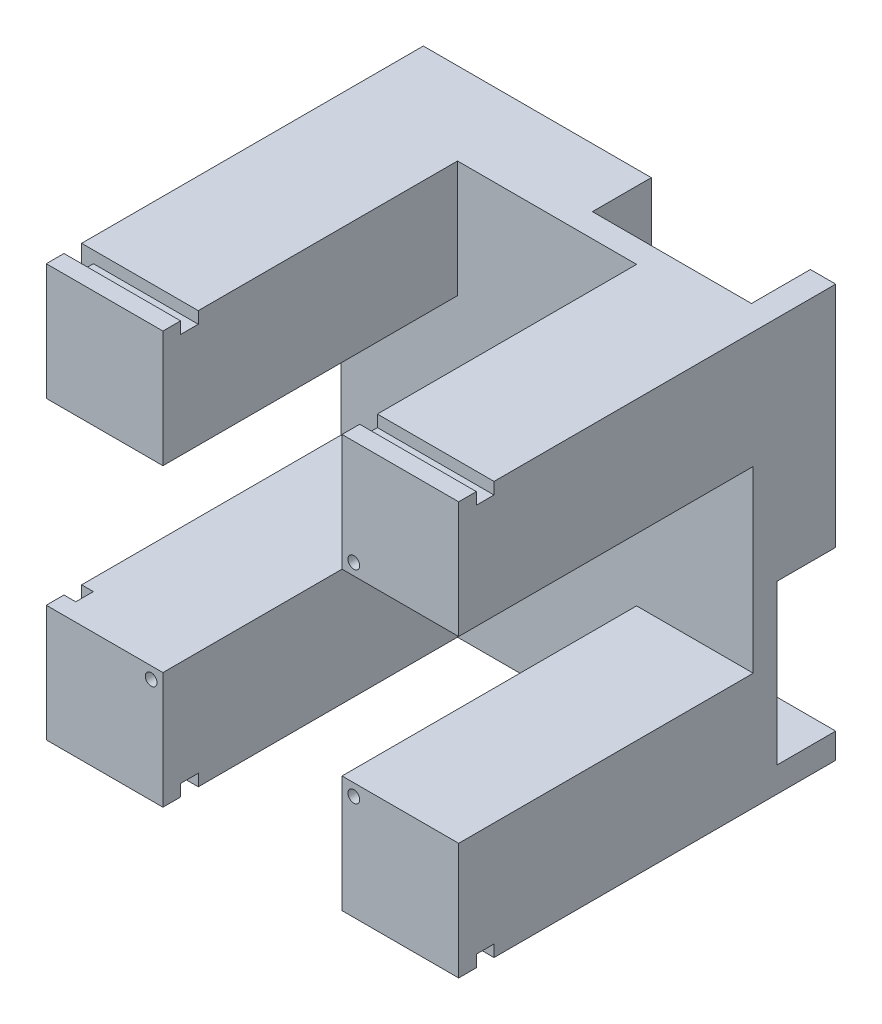
SolidWorks part; units mm, degrees
ref_plane "Plan de face" through (0, 0, 0) normal (0, 0, 1) x (1, 0, 0)
ref_plane "Plan de dessus" through (0, 0, 0) normal (0, 1, 0) x (1, 0, 0)
ref_plane "Plan de droite" through (0, 0, 0) normal (1, 0, 0) x (0, 0, -1)
sketch "Esquisse1" plane through (0, 0, 0) normal (0, 0, 1) x (1, 0, 0)
  line L1 (0, 0) -> (-70, 0)
  line L2 (0, 0) -> (0, 70)
  line L3 (0, 70) -> (-70, 70)
  line L4 (-70, 0) -> (-70, 70)
  dimension "D1" = 70
  dimension "D2" = 70
extrude "Boss.-Extru.1" add sketch "Esquisse1" along normal blind 64
sketch "Esquisse2" plane through (0, 0, 64) normal (0, 0, 1) x (1, 0, 0)
  line L0 (-70, 70) -> (-70, 0) construction
  line L1 (-70, 50.2) -> (0, 50.2)
  line L2 (-70, 50.2) -> (-70, 19.8)
  line L3 (-70, 19.8) -> (0, 19.8)
  line L4 (0, 50.2) -> (0, 19.8)
  line L5 (0, 0) -> (0, 70) construction
  line L6 (-70, 0) -> (0, 0) construction
  line L7 (-19.8, 0) -> (-50.2, 0)
  line L8 (-19.8, 0) -> (-19.8, 70)
  line L9 (-19.8, 70) -> (-50.2, 70)
  line L10 (-50.2, 0) -> (-50.2, 70)
  line L11 (0, 70) -> (-70, 70) construction
  line M5 (0, 0) -> (0, 70)
  line M6 (0, 70) -> (-70, 70)
  line M7 (-70, 70) -> (-70, 0)
  line M8 (-70, 0) -> (0, 0)
  dimension "D1" = 30.4
  dimension "D2" = 19.8
  dimension "D3" = 30.4
  dimension "D4" = 19.8
extrude "Enlèv. mat.-Extru.1" cut sketch "Esquisse2" against normal blind 50 contours L10 L1 L8 M6 | L10 L3 L8 L1 | L8 L3 L1 M5 | L3 L10 L1 M7 | L10 L8 L3 M8
sketch "Esquisse5" plane through (-70, 0, 0) normal (-1, 0, 0) x (0, 0, 1)
  line L0 (64, 70) -> (0, 70) construction
  line L1 (61, 70) -> (58, 70)
  line L2 (61, 70) -> (61, 68)
  line L3 (61, 68) -> (58, 68)
  line L4 (58, 70) -> (58, 68)
  line L5 (64, 0) -> (0, 0) construction
  line L6 (61, 0) -> (58, 0)
  line L7 (61, 0) -> (61, 2)
  line L8 (61, 2) -> (58, 2)
  line L9 (58, 0) -> (58, 2)
  line L10 (64, 19.8) -> (64, 0) construction
  line L11 (64, 70) -> (64, 50.2) construction
  dimension "D1" = 3
  dimension "D2" = 3
  dimension "D3" = 2
  dimension "D4" = 2
  dimension "D5" = 3
  dimension "D6" = 3
extrude "Enlèv. mat.-Extru.3" cut sketch "Esquisse5" against normal through all
sketch "Esquisse6" plane through (0, 70, 0) normal (0, 1, 0) x (1, 0, 0)
  line L0 (-50.2, -61) -> (-70, -61) construction
  line L1 (-70, -58) -> (-68, -58)
  line L2 (-70, -58) -> (-70, -61)
  line L3 (-70, -61) -> (-68, -61)
  line L4 (-68, -58) -> (-68, -61)
  dimension "D1" = 2
extrude "Enlèv. mat.-Extru.4" cut sketch "Esquisse6" against normal through all
sketch "Esquisse7" plane through (0, 0, 64) normal (0, 0, 1) x (1, 0, 0)
  line L0 (-50.2, 0) -> (-50.2, 19.8) construction
  line L1 (-70, 19.8) -> (-50.2, 19.8) construction
  circle A0 centre (-52.2, 17.8) radius 1
  dimension "D1" = 2
  dimension "D2" = 2
  dimension "D3" = 2
extrude "Enlèv. mat.-Extru.5" cut sketch "Esquisse7" against normal through all
sketch "Esquisse8" plane through (0, 0, 0) normal (0, 0, -1) x (-1, 0, 0)
  line L0 (60.2, 17.8) -> (60.2, 0)
  line L1 (70, 0) -> (0, 0) construction
  line L2 (60.2, 0) -> (44.2, 0)
  line L3 (44.2, 0) -> (44.2, 17.8)
  line L4 (44.2, 17.8) -> (60.2, 17.8)
  circle A0 centre (52.2, 17.8) radius 8
  circle M2 centre (52.2, 17.8) radius 1
  line M4 (0, 0) -> (70, 0)
  dimension "D1" = 16
extrude "Enlèv. mat.-Extru.7" cut sketch "Esquisse8" against normal blind 10 contours A0 L3 L0 M4 | L4 A0 M2 | L4 A0 M2
sketch "Esquisse9" plane through (0, 0, 0) normal (0, 0, -1) x (-1, 0, 0)
  line L0 (46.2, 17.8) -> (46.2, 0)
  line L1 (46.2, 0) -> (44.2, 0)
  line L2 (44.2, 0) -> (44.2, 28.7424)
  line L3 (44.2, 28.7424) -> (60.1757, 28.7424)
  line L4 (60.1757, 28.7424) -> (60.2, 17.8)
  line L5 (60.2, 17.8) -> (60.2, 0)
  line L6 (60.2, 17.8) -> (60.2, 0) construction
  line L7 (58.2, 17.8) -> (58.2, 0)
  line L8 (58.2, 0) -> (60.2, 0)
  circle A0 centre (52.2, 17.8) radius 6
  line M1 (60.2, 17.8) -> (60.2, 0)
  line M7 (44.2, 0) -> (44.2, 17.8)
  arc M8 (44.2, 17.8) -> (60.2, 17.8) centre (52.2, 17.8) cw
  dimension "D1" = 12
extrude "Boss.-Extru.2" add sketch "Esquisse9" against normal blind 3.8 contours A0 L7 L8 L1 L0 M1 M8 M7
sketch "Esquisse10" plane through (0, 0, 0) normal (0, 0, -1) x (-1, 0, 0)
  line L0 (70, 0) -> (58.2, 0) construction
  line L1 (38.7, 18.1) -> (65.7, 18.1)
  line L2 (38.7, 18.1) -> (38.7, 0)
  line L3 (38.7, 0) -> (65.7, 0)
  line L4 (65.7, 18.1) -> (65.7, 0)
  arc A0 (58.1926, 18.098) -> (46.2076, 18.1013) centre (52.2, 17.8) ccw
  arc A2 (58.2, 17.8) -> (46.2, 17.8) centre (52.2, 17.8) ccw construction
  line M3 (58.2, 17.8) -> (58.2, 0)
  line M4 (58.2, 0) -> (70, 0)
  line M8 (0, 0) -> (46.2, 0)
  line M9 (46.2, 0) -> (46.2, 17.8)
  dimension "D1" = 27
  dimension "D2" = 5.5
extrude "Enlèv. mat.-Extru.8" cut sketch "Esquisse10" against normal blind 10 contours L1 L2 M8 M9 | L4 L1 M3 M4
sketch "Esquisse11" plane through (0, 18.1, 0) normal (0, -1, 0) x (1, 0, 0)
  line L0 (-38.7, 10) -> (-38.7, 0) construction
  line L1 (-65.7, 10) -> (-65.7, 0) construction
  line L2 (-60.1944, 10) -> (-65.7, 10) construction
  line L3 (-38.7, 10) -> (-44.2056, 10) construction
  circle A0 centre (-41.7, 7) radius 1.25
  circle A1 centre (-62.7, 7) radius 1.25
  dimension "D1" = 2.5
  dimension "D2" = 2.5
  dimension "D3" = 3
  dimension "D4" = 3
  dimension "D5" = 3
  dimension "D6" = 3
extrude "Enlèv. mat.-Extru.9" cut sketch "Esquisse11" against normal blind 15
sketch3d "Esquisse3D2"
  line L0 (-35, 35, 57.383) -> (-35, 35, -1.6203) construction
  point P2 (0, 35, 0)
  point P5 (0, 35, 64)
  dimension "D1" = 35
  dimension "D2" = 35
  dimension "D3" = 35
pattern_circular "Répétition circulaire1" count 3 every 90 about axis through (-35, 35, 0) along (0, 0, 1) of "Enlèv. mat.-Extru.5", "Enlèv. mat.-Extru.7", "Enlèv. mat.-Extru.8"
